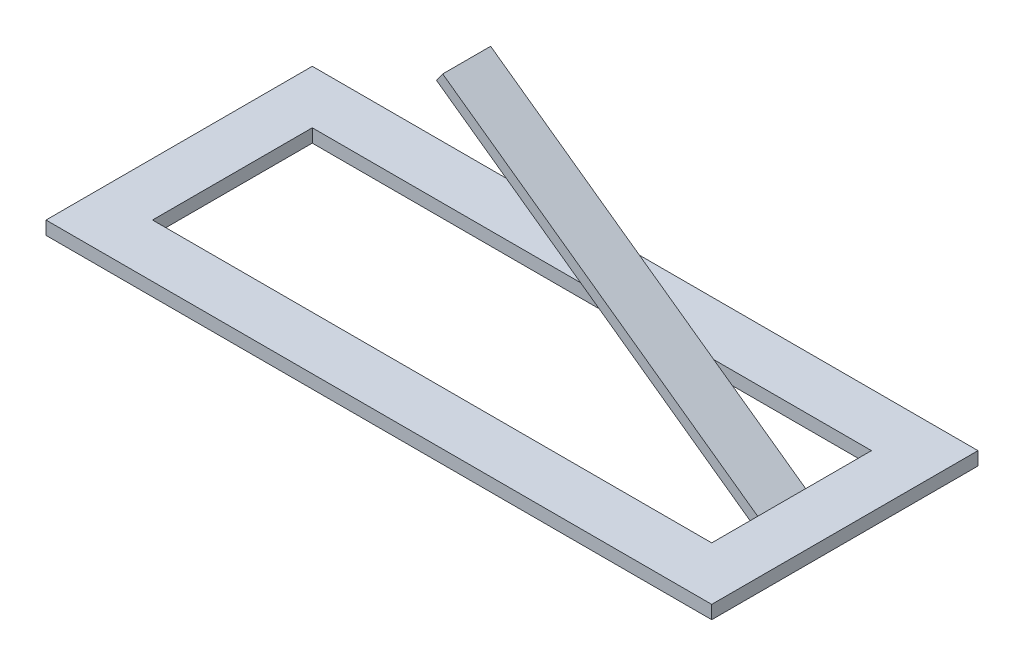
SolidWorks part; units mm, degrees
ref_plane "Front Plane" through (0, 0, 0) normal (0, 0, 1) x (1, 0, 0)
ref_plane "Top Plane" through (0, 0, 0) normal (0, 1, 0) x (1, 0, 0)
ref_plane "Right Plane" through (0, 0, 0) normal (1, 0, 0) x (0, 0, -1)
sketch "Sketch1" plane through (0, 0, 0) normal (0, 1, 0) x (1, 0, 0)
  line L0 (-63.7778, 60) -> (146.2222, 60)
  line L1 (-83.7778, 80) -> (166.2222, 80)
  line L2 (-83.7778, 80) -> (-83.7778, 60)
  line L4 (166.2222, 80) -> (166.2222, 60)
  line L6 (-83.7778, 0) -> (-83.7778, -20)
  line L7 (-83.7778, -20) -> (166.2222, -20)
  line L8 (166.2222, 0) -> (166.2222, -20)
  line L9 (-83.7778, 60) -> (-63.7778, 60)
  line L10 (-83.7778, 60) -> (-83.7778, 0)
  line L11 (-83.7778, 0) -> (-63.7778, 0)
  line L12 (-63.7778, 60) -> (-63.7778, 0)
  line L13 (166.2222, 60) -> (146.2222, 60)
  line L14 (166.2222, 60) -> (166.2222, 0)
  line L15 (166.2222, 0) -> (146.2222, 0)
  line L16 (146.2222, 60) -> (146.2222, 0)
  line L17 (146.2222, 0) -> (-63.7778, 0)
  dimension "D1" = 20
  dimension "D2" = 20
  dimension "D3" = 20
  dimension "D4" = 250
  dimension "D5" = 250
  dimension "D6" = 20
extrude "Boss-Extrude2" add sketch "Sketch1" along normal blind 10 contours L13 L4 L1 L2 L9 L0 | L13 L16 L15 L14 | L15 L17 L11 L6 L7 L8 | L12 L9 L10 L11
sketch "Sketch2" plane through (0, 0, 0) normal (0, 0, 1) x (1, 0, 0)
  line L0 (155.308, 2.2662) -> (27.1984, 93.9992)
  line L1 (27.1984, 93.9992) -> (24.8697, 90.7469)
  line L2 (24.8697, 90.7469) -> (148.4373, 2.2662)
  line L3 (148.4373, 2.2662) -> (155.308, 2.2662)
  dimension "D1" = 4
extrude "Boss-Extrude3" add sketch "Sketch2" against normal blind 36
sketch "Sketch3" plane through (0, 0, 0) normal (0, 0, 1) x (1, 0, 0)
  line L2 (152.1947, 10) -> (12.1947, 10)
  line L3 (152.1947, 10) -> (152.1947, 150)
  line L4 (152.1947, 150) -> (12.1947, 150)
  line L5 (12.1947, 10) -> (12.1947, 150)
  dimension "D1" = 140
  dimension "D2" = 140
extrude "Cut-Extrude1" cut sketch "Sketch3" against normal blind 18
sketch "Sketch4" plane through (0, 10, 0) normal (0, 1, 0) x (1, 0, 0)
  line L1 (137.6367, 18) -> (146.2222, 18)
  line L2 (137.6367, 18) -> (137.6367, 0)
  line L3 (137.6367, 0) -> (146.2222, 0)
  line L4 (146.2222, 18) -> (146.2222, 0)
extrude "Cut-Extrude3" cut sketch "Sketch4" against normal blind 46
sketch "Sketch5" plane through (0, 0, 20) normal (0, 0, 1) x (1, 0, 0)
  line L0 (-83.7778, 5) -> (166.2222, 5)
  line L1 (-83.7778, 10) -> (-83.7778, 0) construction
  line L2 (166.2222, 10) -> (166.2222, 0) construction
  line L4 (-83.7778, 5) -> (166.2222, 5)
  line L5 (-83.7778, 5) -> (-83.7778, 0)
  line L6 (-83.7778, 0) -> (166.2222, 0)
  line L7 (166.2222, 5) -> (166.2222, 0)
sketch "Sketch6" plane through (166.2222, 0, 0) normal (1, 0, 0) x (0, 0, -1)
  line L0 (-20, 5) -> (80, 5)
  line L1 (-20, 10) -> (-20, 0) construction
  line L2 (80, 10) -> (80, 0) construction
sketch "Sketch7" plane through (0, 0, -80) normal (0, 0, -1) x (-1, 0, 0)
  line L0 (-166.2222, 5) -> (83.7778, 5)
  line L1 (-166.2222, 10) -> (-166.2222, 0) construction
  line L2 (83.7778, 10) -> (83.7778, 0) construction
sketch "Sketch8" plane through (-83.7778, 0, 0) normal (-1, 0, 0) x (0, 0, 1)
  line L0 (-80, 5) -> (20, 5)
  line L1 (-80, 10) -> (-80, 0) construction
extrude "Cut-Extrude4" cut sketch "Sketch5" against normal blind 137 contours L5 L4 L7 L6
